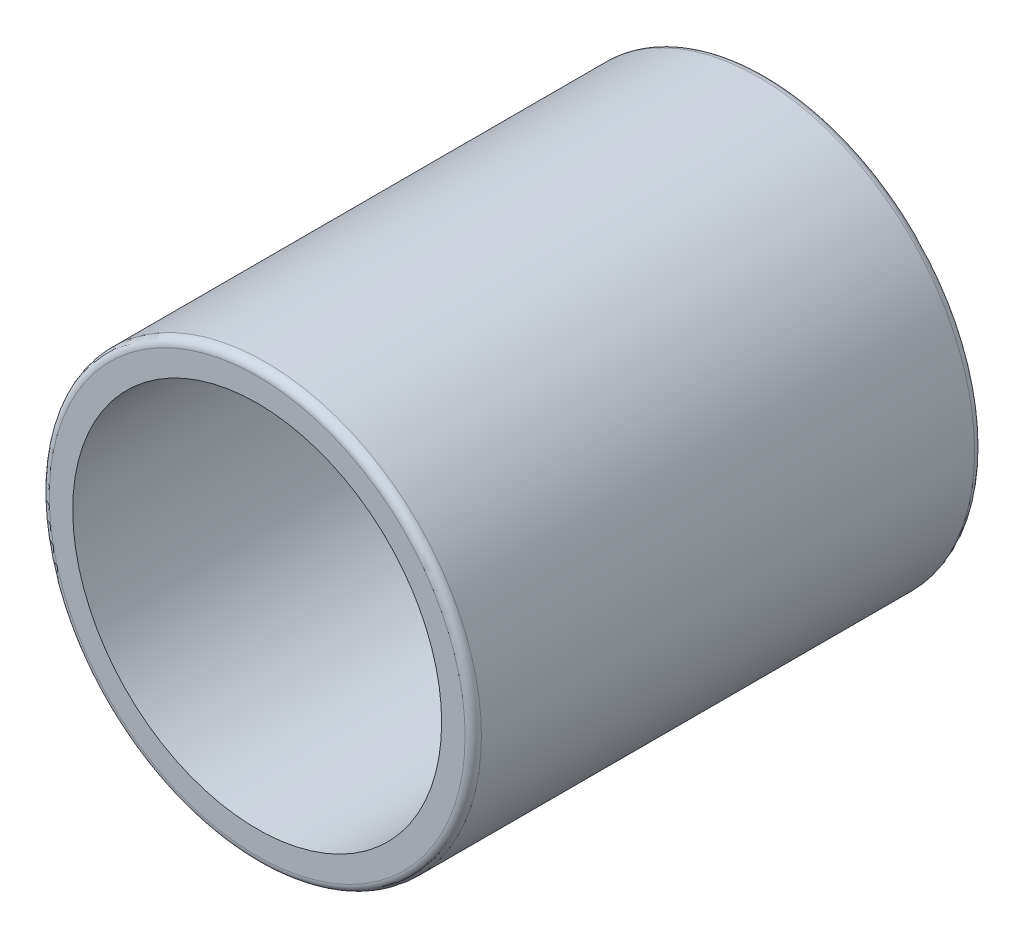
SolidWorks part; units mm, degrees
ref_plane "Front" through (0, 0, 0) normal (0, 0, 1) x (1, 0, 0)
ref_plane "Top" through (0, 0, 0) normal (0, 1, 0) x (1, 0, 0)
ref_plane "Right" through (0, 0, 0) normal (1, 0, 0) x (0, 0, -1)
sketch "草图1" plane through (0, 0, 0) normal (0, 0, 1) x (1, 0, 0)
  circle A0 centre (0, 0) radius 4.525
  circle A1 centre (0, 0) radius 5.3
  dimension "D1" = 9.05
  dimension "D2" = 10.6
extrude "凸台-拉伸1" add sketch "草图1" along normal blind 12.5
sketch "草图2" plane through (0, 0, 0) normal (1, 0, 0) x (0, 0, -1)
  line L2 (-3, 2.5) -> (0.9704, 2.5)
  line L3 (-3, 2.5) -> (-3, -2.5)
  line L4 (-3, -2.5) -> (0.9704, -2.5)
  line L5 (0.9704, 2.5) -> (0.9704, -2.5)
  circle A0 centre (-3, 0) radius 1.6
  circle A1 centre (-3, 0) radius 2.5
  dimension "D1" = 3.2
  dimension "D2" = 5
  dimension "D3" = 5
  dimension "D4" = 3
extrude "切除-拉伸1" cut sketch "草图2" against normal blind 12.5 contours A1 | L2 L5 L4 L3
fillet "圆角1" radius 0.2 2 edges at (5.3, 0, 0) (5.3, 0, 12.5)
